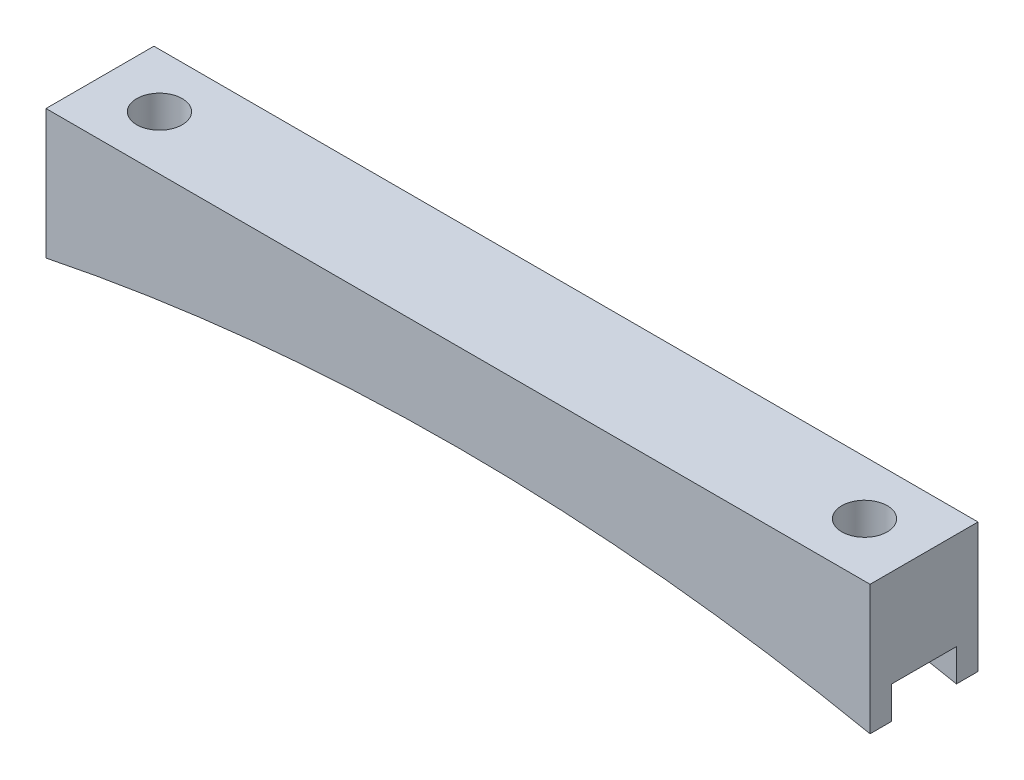
SolidWorks part; units mm, degrees
ref_plane "Front Plane" through (0, 0, 0) normal (0, 0, 1) x (1, 0, 0)
ref_plane "Top Plane" through (0, 0, 0) normal (0, 1, 0) x (1, 0, 0)
ref_plane "Right Plane" through (0, 0, 0) normal (1, 0, 0) x (0, 0, -1)
sketch "Sketch1" plane through (0, 0, 0) normal (0, 0, 1) x (1, 0, 0)
  line L0 (-48.485, 0) -> (48.485, 0)
  line L1 (-41.485, -2.54) -> (41.485, -2.54) construction
  line L2 (0, 0) -> (0, -4.6068) construction
  line L3 (48.485, 0) -> (48.485, -15.24)
  line L4 (-48.485, 0) -> (-48.485, -15.24)
  arc A0 (-48.485, -15.24) -> (48.485, -15.24) centre (0, -251.6187) cw
  point P4 (0, 0)
  point P9 (0, -2.54)
  dimension "D4" = 241.3
  dimension "D1" = 82.97
  dimension "D2" = 2.54
  dimension "D3" = 7
  dimension "D5" = 15.24
extrude "Boss-Extrude1" add sketch "Sketch1" along normal blind 12.7
sketch "Sketch2" plane through (0, 0, 0) normal (0, 1, 0) x (1, 0, 0)
  line L1 (-41.485, 0) -> (-41.485, -12.7) construction
  line L2 (-48.485, 0) -> (48.485, 0) construction
  line L3 (48.485, -12.7) -> (-48.485, -12.7) construction
  line L4 (41.485, 0) -> (41.485, -12.7) construction
  circle A0 centre (-41.485, -6.35) radius 2.675
  circle A1 centre (41.485, -6.35) radius 2.675
  circle A2 centre (-41.485, -6.35) radius 3 construction
  point P7 (-41.485, -6.35)
  dimension "D1" = 5.35
  dimension "D2" = 6
extrude "Cut-Extrude1" cut sketch "Sketch2" against normal through all
sketch "Sketch3" plane through (48.485, 0, 0) normal (1, 0, 0) x (0, 0, -1)
  line L0 (-12.7, -15.24) -> (0, -15.24) construction
  line L1 (-10.16, -15.24) -> (-2.54, -15.24)
  line L2 (-10.16, -15.24) -> (-10.16, -11.43)
  line L3 (-10.16, -11.43) -> (-2.54, -11.43)
  line L4 (-2.54, -15.24) -> (-2.54, -11.43)
  line L5 (-12.7, -15.24) -> (-12.7, 0) construction
  line L6 (0, -15.24) -> (0, 0) construction
  dimension "D1" = 2.54
  dimension "D2" = 2.54
  dimension "D3" = 3.81
extrude "Cut-Extrude2" cut sketch "Sketch3" against normal through all
